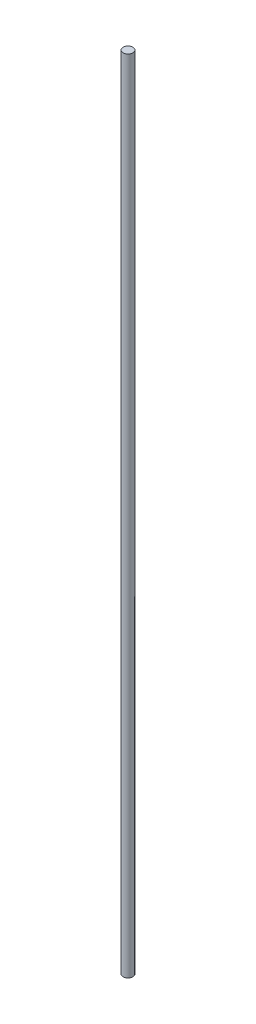
SolidWorks part; units mm, degrees
ref_plane "Alzado" through (0, 0, 0) normal (0, 0, 1) x (1, 0, 0)
ref_plane "Planta" through (0, 0, 0) normal (0, 1, 0) x (1, 0, 0)
ref_plane "Vista lateral" through (0, 0, 0) normal (1, 0, 0) x (0, 0, -1)
sketch "Croquis1" plane through (0, 0, 0) normal (0, 1, 0) x (1, 0, 0)
  circle A0 centre (0, 0) radius 6.35
  dimension "D1" = 12.7
sketch "Croquis2" plane through (0, 0, 0) normal (0, 0, 1) x (1, 0, 0)
  line L0 (0, 0) -> (0, 1040)
  dimension "D1" = 1040
sweep "Barrer1" add profiles "Croquis1" path "Croquis2"
